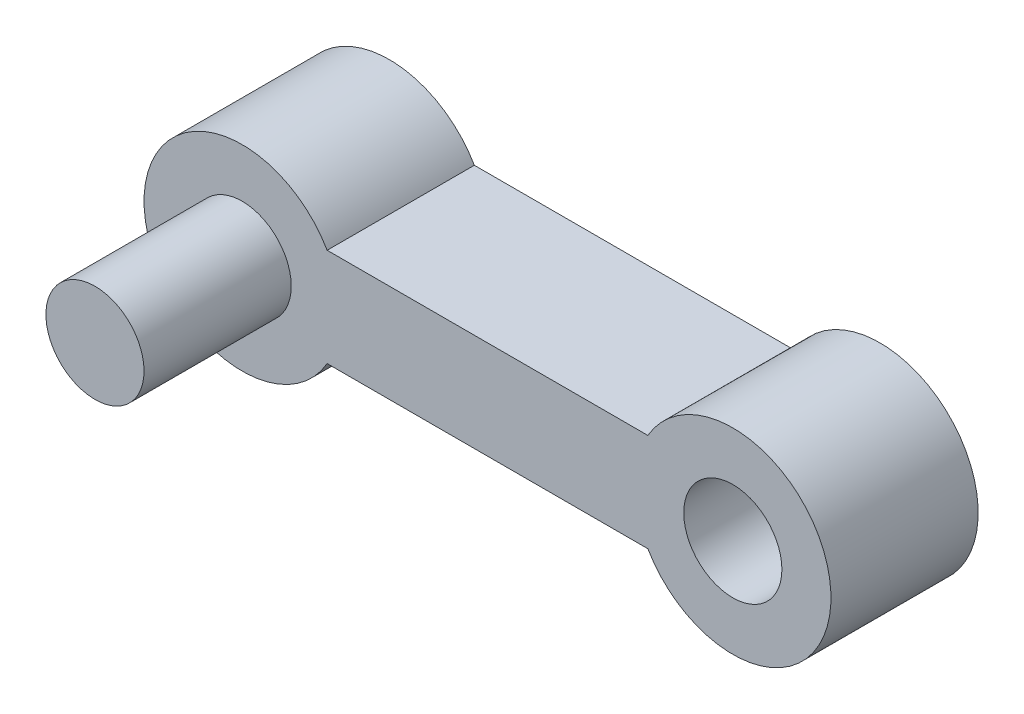
SolidWorks part; units mm, degrees
ref_plane "Спереди" through (0, 0, 0) normal (0, 0, 1) x (1, 0, 0)
ref_plane "Сверху" through (0, 0, 0) normal (0, 1, 0) x (1, 0, 0)
ref_plane "Справа" through (0, 0, 0) normal (1, 0, 0) x (0, 0, -1)
other "Configuration Table"
sketch "Sketch2" plane through (0, 0, 0) normal (0, 0, 1) x (1, 0, 0)
  line L1 (-36.505, 13.8003) -> (-29.9691, 13.8003)
  line L5 (-36.505, 11.8003) -> (-29.9691, 11.8003)
  line L7 (-13.5959, 12.8003) -> (-45.3291, 12.8003) construction
  arc A0 (-36.505, 13.8003) -> (-36.505, 11.8003) centre (-38.2371, 12.8003) ccw
  arc A2 (-29.9691, 13.8003) -> (-29.9691, 11.8003) centre (-28.2371, 12.8003) cw
  dimension "D3" = 4
  dimension "D1" = 2
  dimension "D2" = 10
extrude "Boss-Extrude1" add sketch "Sketch2" along normal blind 3
ref_plane "Plane1" through (0, 0, 3) normal (0, 0, 1) x (1, 0, 0)
sketch "Sketch3" plane through (0, 0, 3) normal (0, 0, 1) x (1, 0, 0)
  circle A0 centre (-38.2371, 12.8003) radius 1
  dimension "D1" = 2
extrude "Boss-Extrude2" add sketch "Sketch3" along normal blind 3
ref_plane "Plane2" through (0, 0, 0) normal (0, 0, -1) x (-1, 0, 0)
sketch "Sketch4" plane through (0, 0, 0) normal (0, 0, -1) x (-1, 0, 0)
  circle A0 centre (28.2371, 12.8003) radius 1
  circle A1 centre (38.2371, 12.8003) radius 1 construction
extrude "Cut-Extrude1" cut sketch "Sketch4" against normal up to surface (3 mm away) up to face at (-37.2371, 12.8003, 3)
equation "\"R small\"= 2"
equation "\"R big\"= 4"
equation "\"width\"= 0.6"
equation "\"border width\"= 1"
equation "\"D3@Sketch2\"=\"R big\""
equation "\"D1@Sketch2\"=\"R small\""
equation "\"D1@Sketch3\"=\"R small\""
